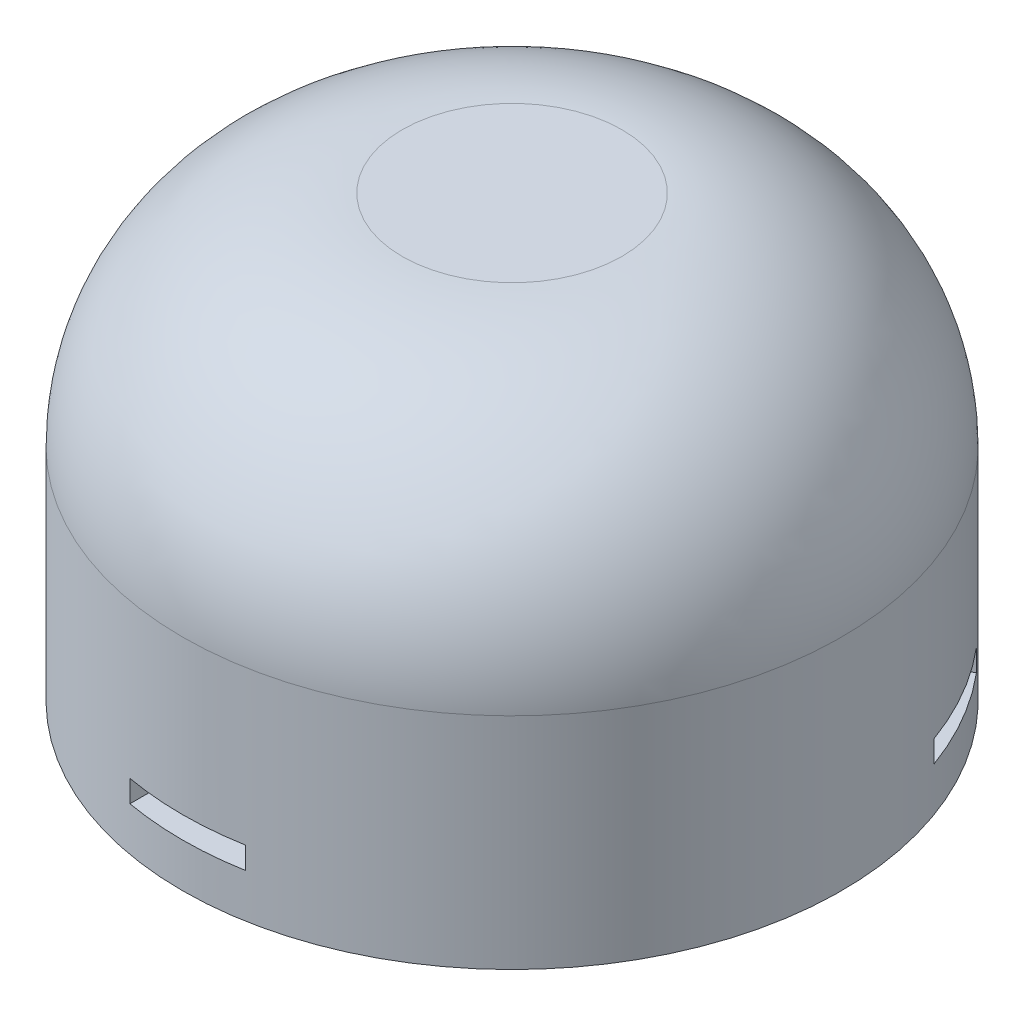
SolidWorks part; units mm, degrees
ref_plane "Front Plane" through (0, 0, 0) normal (0, 0, 1) x (1, 0, 0)
ref_plane "Top Plane" through (0, 0, 0) normal (0, 1, 0) x (1, 0, 0)
ref_plane "Right Plane" through (0, 0, 0) normal (1, 0, 0) x (0, 0, -1)
sketch "Sketch1" plane through (0, 0, 0) normal (0, 1, 0) x (1, 0, 0)
  circle A0 centre (0, 0) radius 15
  dimension "D1" = 30
extrude "Boss-Extrude1" add sketch "Sketch1" along normal blind 20
fillet "Fillet1" radius 10 1 edges at (0, 20, 15)
sketch "Sketch2" plane through (0, 0, 0) normal (0, 0, 1) x (1, 0, 0)
  line L0 (-15, 0) -> (15, 0) construction
  line L1 (-2.625, 2) -> (2.625, 2)
  line L2 (-2.625, 2) -> (-2.625, 3)
  line L3 (-2.625, 3) -> (2.625, 3)
  line L4 (2.625, 2) -> (2.625, 3)
  point P4 (0, 2)
  dimension "D1" = 5.25
  dimension "D2" = 1
  dimension "D3" = 2
extrude "Cut-Extrude1" cut sketch "Sketch2" against normal blind 30 from offset 40
pattern_circular "CirPattern1" count 3 over 360 about axis through (0, 0, 0) along (0, 1, 0) of "Cut-Extrude1"
